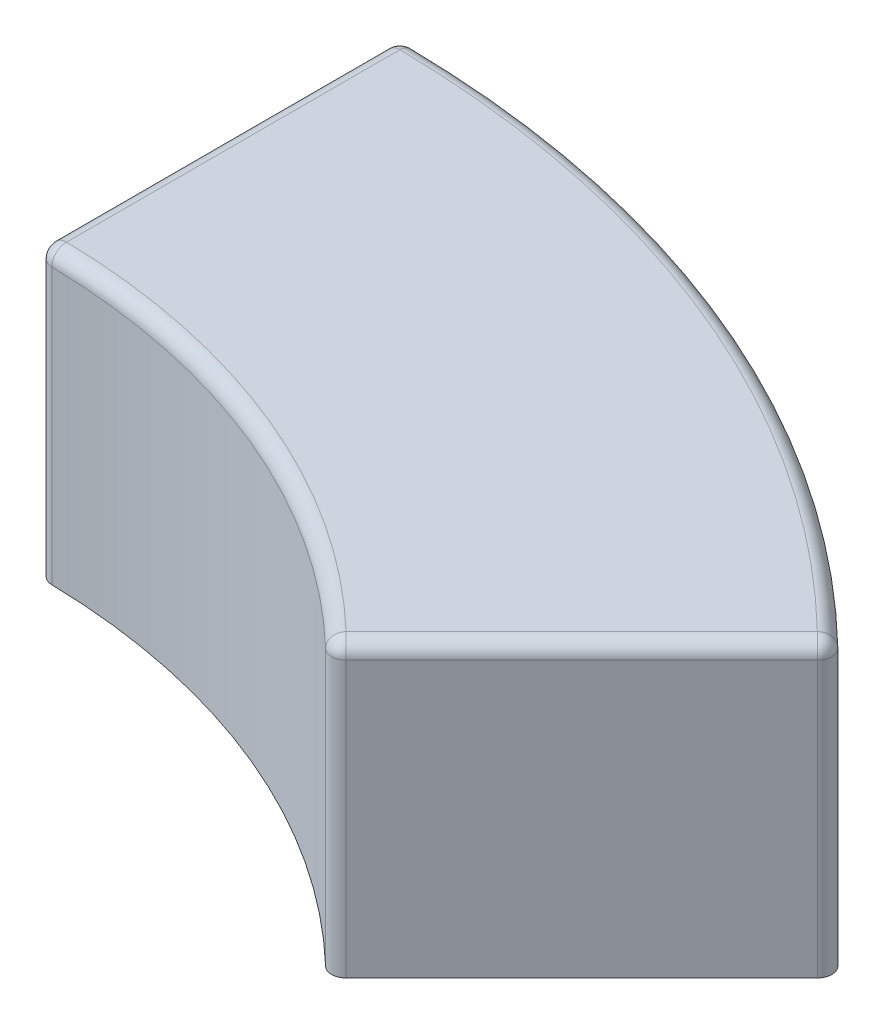
SolidWorks part; units mm, degrees
material "AISI 1020"
ref_plane "Front Plane" through (0, 0, 0) normal (0, 0, 1) x (1, 0, 0)
ref_plane "Top Plane" through (0, 0, 0) normal (0, 1, 0) x (1, 0, 0)
ref_plane "Right Plane" through (0, 0, 0) normal (1, 0, 0) x (0, 0, -1)
sketch "Sketch1" plane through (0, 0, 0) normal (0, 1, 0) x (1, 0, 0)
  line L0 (0, 960) -> (0, 1460)
  line L1 (678.8225, 678.8225) -> (1032.3759, 1032.3759)
  arc A2 (0, 1460) -> (1032.3759, 1032.3759) centre (0, 0) cw
  arc A3 (0, 960) -> (678.8225, 678.8225) centre (0, 0) cw
extrude "Boss-Extrude1" add sketch "Sketch1" along normal blind 400
fillet "Fillet1" radius 20 8 edges at (558.7178, 400, -1348.8641) (1032.3759, 200, -1032.3759) (0, 200, -1460) (0, 400, -1210) (0, 200, -960) (367.3761, 400, -886.9244) (855.5992, 400, -855.5992) (678.8225, 200, -678.8225)
sketch "Sketch3" plane through (0, 400, 0) normal (0, 1, 0) x (1, 0, 0)
  line L1 (0, 0) -> (1417.2815, -587.0572) construction
sketch "Sketch4" plane through (0, 400, 0) normal (0, 1, 0) x (1, 0, 0)
  line L0 (20, 1439.8611) -> (20, 979.7959)
  line L1 (678.6782, 706.9625) -> (1003.9934, 1032.2777) construction
  line L2 (678.6782, 706.9625) -> (1003.9934, 1032.2777)
  arc A0 (20, 979.7959) -> (678.6782, 706.9625) centre (0, 0) cw
  arc A1 (20, 1439.8611) -> (1003.9934, 1032.2777) centre (0, 0) cw
  line M1 (678.6782, 706.9625) -> (1003.9934, 1032.2777)
  arc M2 (1003.9934, 1032.2777) -> (20, 1439.8611) centre (0, 0) ccw
  line M3 (20, 1439.8611) -> (20, 979.7959)
  arc M4 (20, 979.7959) -> (678.6782, 706.9625) centre (0, 0) cw
extrude "Cut-Extrude1" cut sketch "Sketch4" against normal blind 360 from offset 20 contours M4 M1 M2 M3
